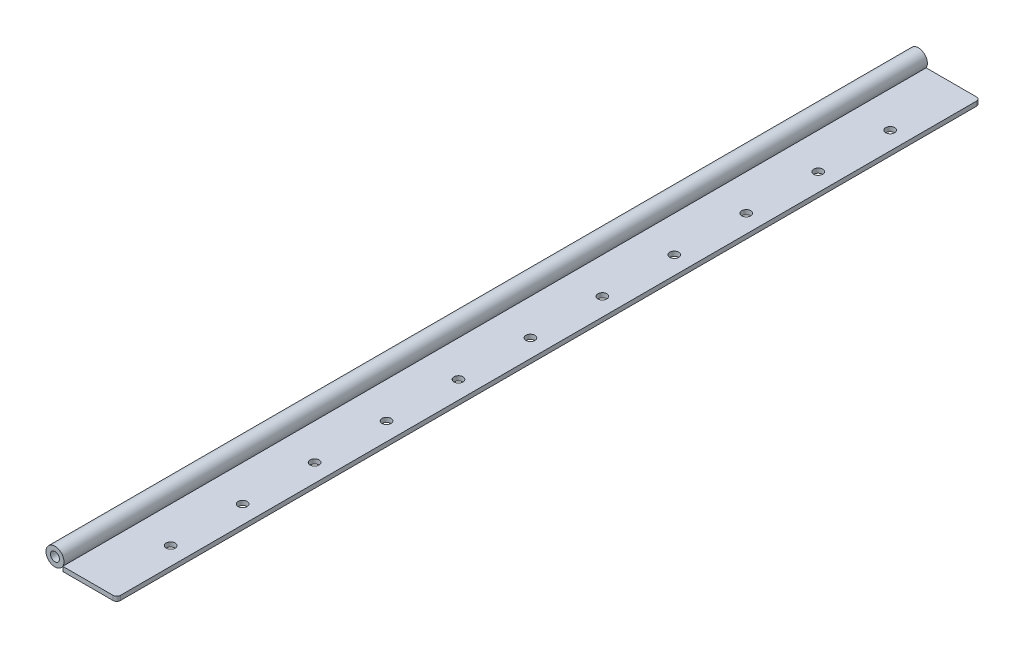
SolidWorks part; units mm, degrees
ref_plane "Front Plane" through (0, 0, 0) normal (0, 0, 1) x (1, 0, 0)
ref_plane "Top Plane" through (0, 0, 0) normal (0, 1, 0) x (1, 0, 0)
ref_plane "Right Plane" through (0, 0, 0) normal (1, 0, 0) x (0, 0, -1)
sketch "Sketch1" plane through (0, 0, 0) normal (0, 1, 0) x (1, 0, 0)
  line L1 (0, 0) -> (38.1, 0)
  line L2 (0, 0) -> (0, 609.6)
  line L3 (0, 609.6) -> (38.1, 609.6)
  line L4 (38.1, 0) -> (38.1, 609.6)
  dimension "D1" = 38.1
  dimension "D2" = 609.6
extrude "Boss-Extrude1" add sketch "Sketch1" along normal blind 3.175
sketch "Sketch2" plane through (0, 3.175, 0) normal (0, 1, 0) x (-1, 0, 0)
  line L0 (-38.1, 0) -> (-38.1, -609.6) construction
  line L1 (-38.1, -304.8) -> (0, -304.8) construction
  line L2 (0, -609.6) -> (0, 0) construction
  circle A0 centre (-25.4, -355.6) radius 3.175
  circle A1 centre (-25.4, -304.8) radius 3.175
  circle A2 centre (-25.4, -254) radius 3.175
  circle A3 centre (-25.4, -406.4) radius 3.175
  circle A4 centre (-25.4, -457.2) radius 3.175
  circle A5 centre (-25.4, -508) radius 3.175
  circle A6 centre (-25.4, -558.8) radius 3.175
  circle A7 centre (-25.4, -101.6) radius 3.175
  circle A8 centre (-25.4, -50.8) radius 3.175
  circle A10 centre (-25.4, -203.2) radius 3.175
  circle A11 centre (-25.4, -152.4) radius 3.175
  circle A17 centre (-25.4, -101.6) radius 3.175 [skipped]
  circle A18 centre (-25.4, -50.8) radius 3.175 [skipped]
  circle A19 centre (-25.4, 0) radius 3.175 [skipped]
  circle A20 centre (-25.4, 50.8) radius 3.175 [skipped]
  circle A21 centre (-25.4, 101.6) radius 3.175 [skipped]
  circle A22 centre (-25.4, -508) radius 3.175 [skipped]
  circle A23 centre (-25.4, -558.8) radius 3.175 [skipped]
  circle A24 centre (-25.4, -609.6) radius 3.175 [skipped]
  circle A25 centre (-25.4, -660.4) radius 3.175 [skipped]
  circle A26 centre (-25.4, -711.2) radius 3.175 [skipped]
  dimension "D4" = 6.35
  dimension "D3" = 50.8
  dimension "D1" = 12.7
  dimension "D2" = 12.7
  dimension "D5" = 8
  dimension "D6" = 8
  dimension "D7" = 3
  dimension "D8" = 3
extrude "Cut-Extrude1" cut sketch "Sketch2" against normal up to next
fillet "Fillet1" radius 2.54 2 edges at (38.1, 1.5875, 0) (38.1, 1.5875, -609.6)
sketch "Sketch3" plane through (0, 0, 0) normal (0, 0, 1) x (1, 0, 0)
  line L0 (0, 0) -> (35.56, 0) construction
  circle A0 centre (-5.4993, 6.35) radius 6.35
  circle A1 centre (-5.4993, 6.35) radius 3.175
  dimension "D1" = 12.7
  dimension "D2" = 6.35
extrude "Boss-Extrude2" add sketch "Sketch3" against normal blind 609.6 separate body
